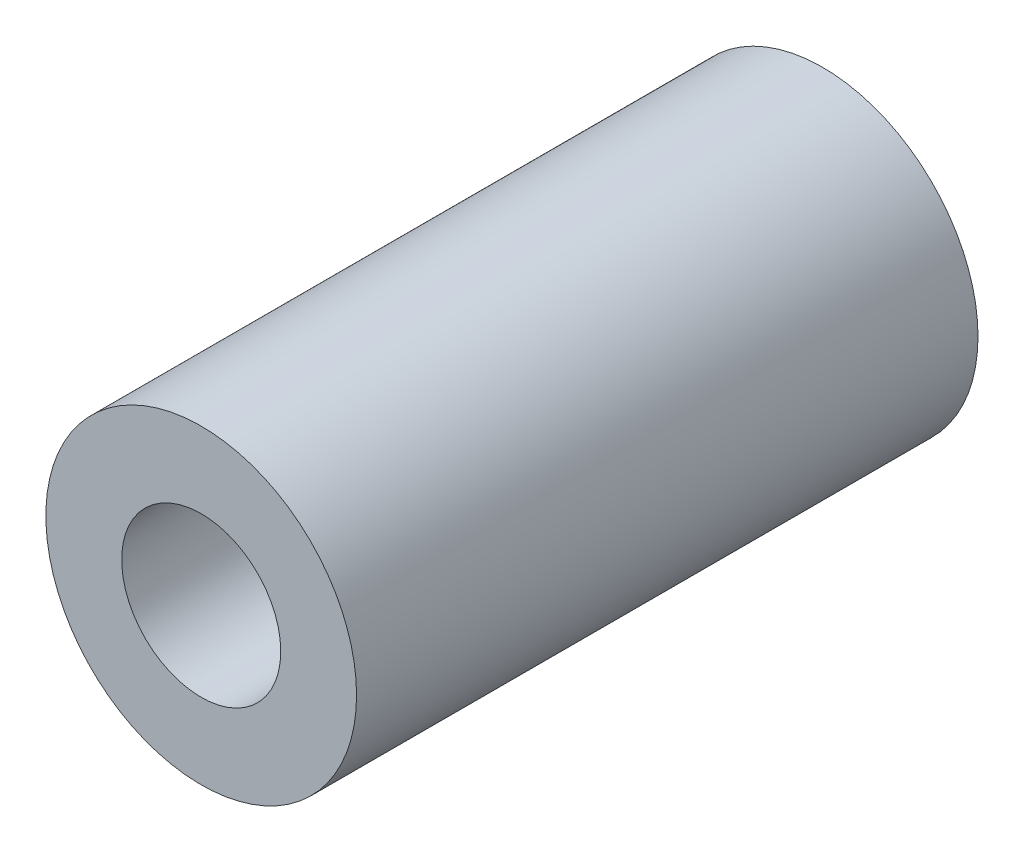
SolidWorks part; units mm, degrees
ref_plane "Front Plane" through (0, 0, 0) normal (0, 0, 1) x (1, 0, 0)
ref_plane "Top Plane" through (0, 0, 0) normal (0, 1, 0) x (1, 0, 0)
ref_plane "Right Plane" through (0, 0, 0) normal (1, 0, 0) x (0, 0, -1)
sketch "Sketch1" plane through (0, 0, 0) normal (0, 0, 1) x (1, 0, 0)
  circle A0 centre (0, 0) radius 4.7625
  circle A1 centre (0, 0) radius 2.4384
  dimension "OD" = 9.525
  dimension "ID" = 4.8768
extrude "Extrude1" add sketch "Sketch1" along normal mid plane 19.05
sketch "Sketch2" plane through (0, 0, 0) normal (1, 0, 0) x (0, 0, -1)
  line L0 (-9.525, -2.4384) -> (9.525, -2.4384) construction
  line L3 (9.525, 2.4384) -> (-9.525, 2.4384) construction
  line L5 (-9.525, -2.4384) -> (9.525, -2.4384)
  line L6 (9.525, 2.4384) -> (-9.525, 2.4384)
sketch "Sketch4" plane through (0, 0, 9.525) normal (0, 0, 1) x (1, 0, 0)
  line L0 (0, 0) -> (-1.7242, 1.7242)
  line L1 (0, -2.1828) -> (0, 2.1828) construction
  circle A0 centre (0, 0) radius 2.4384 construction
  dimension "D1" = 45
